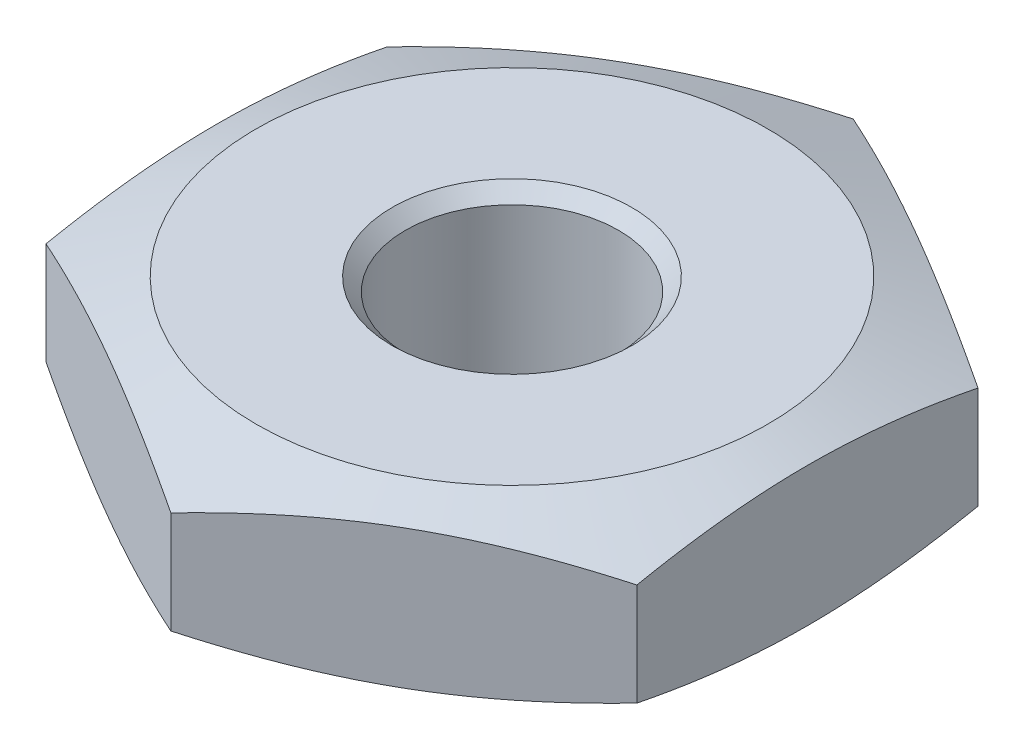
SolidWorks part; units mm, degrees
material "镀铬不锈钢"
ref_plane "前视基准面" through (0, 0, 0) normal (0, 0, 1) x (1, 0, 0)
ref_plane "上视基准面" through (0, 0, 0) normal (0, 1, 0) x (1, 0, 0)
ref_plane "右视基准面" through (0, 0, 0) normal (1, 0, 0) x (0, 0, -1)
sketch "草图1" plane through (0, 0, 0) normal (0, 1, 0) x (1, 0, 0)
  line L1 (0, -20) -> (17.3205, -10)
  line L2 (17.3205, -10) -> (17.3205, 10)
  line L3 (17.3205, 10) -> (0, 20)
  line L4 (0, 20) -> (-17.3205, 10)
  line L5 (-17.3205, 10) -> (-17.3205, -10)
  line L6 (-17.3205, -10) -> (0, -20)
  circle A0 centre (0, 0) radius 17.3205 construction
  dimension "D1" = 20
extrude "凸台-拉伸1" add sketch "草图1" along normal blind 10 contours L1 L2 L3 L4 L5 L6
hole_wizard "M14x1.5 螺纹孔1" positions "草图4" profile "草图6" tap size "M14x1.5" standard "GB" end condition through all
sketch "草图4" plane through (0, 10, 0) normal (0, 1, 0) x (1, 0, 0)
  point P0 (0, 0)
sketch "草图6" plane through (0, 10, 0) normal (1, 0, 0) x (0, 0, 1)
  line L0 (0, 0) -> (0, 10)
  line L1 (0, 10) -> (6.25, 10)
  line L2 (6.25, 10) -> (6.25, 0.775)
  line L3 (6.25, 0.775) -> (7.025, 0)
  line L5 (7.025, 0) -> (0, 0)
  line L6 (-6.25, 0.775) -> (-7.025, 0) construction
  line L11 (0, -6.35) -> (0, 107.95) construction
  dimension "通孔螺纹孔钻头直径" = 12.5
  dimension "通孔螺纹孔钻头深度" = 10
  dimension "近端锥形沉头孔直径" = 14.05
  dimension "近端锥形沉头孔角度" = 90
cosmetic thread "孔螺蚊线1" parameters "D2"=14
sketch "草图7" plane through (0, 0, 0) normal (1, 0, 0) x (0, 0, -1)
  line L0 (20, 10) -> (20, 8)
  line L1 (20, 10) -> (20, 0) construction
  line L2 (20, 8) -> (15, 10)
  line L3 (10, 10) -> (20, 10) construction
  line L4 (15, 10) -> (20, 10)
  line L5 (20, 2) -> (15, 0)
  line L6 (19.0526, 0) -> (-19.0526, 0) construction
  line L7 (15, 0) -> (20, 0)
  line L8 (20, 0) -> (20, 2)
  line L9 (0, 15.716) -> (0, -49984.284) construction
  line L10 (0, 5.5) -> (0, -5.5) construction
  line L11 (20, 5) -> (-49980, 5) construction
  point P15 (20, 5)
  dimension "D1" = 6
  dimension "D2" = 5
revolve "切除-旋转1" cut sketch "草图7" angle 360 about L9
